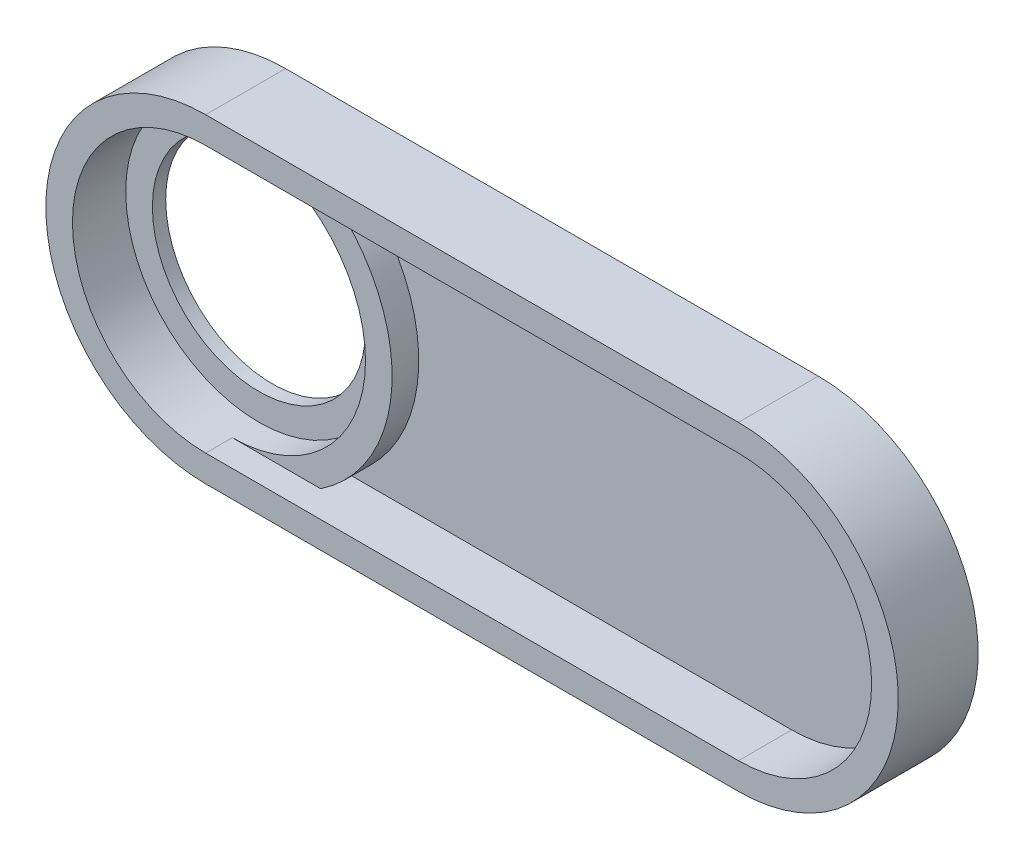
SolidWorks part; units mm, degrees
ref_plane "Front Plane" through (0, 0, 0) normal (0, 0, 1) x (1, 0, 0)
ref_plane "Top Plane" through (0, 0, 0) normal (0, 1, 0) x (1, 0, 0)
ref_plane "Right Plane" through (0, 0, 0) normal (1, 0, 0) x (0, 0, -1)
sketch "Sketch1" plane through (0, 0, 0) normal (0, 0, 1) x (1, 0, 0)
  line L0 (0, 0) -> (200, 0) construction
  line L1 (0, 60) -> (200, 60)
  line L2 (0, -60) -> (200, -60)
  arc A0 (0, 60) -> (0, -60) centre (0, 0) ccw
  arc A1 (200, -60) -> (200, 60) centre (200, 0) ccw
  circle A2 centre (0, 0) radius 40
  point P2 (100, 0)
  dimension "D3" = 80
  dimension "D1" = 60
  dimension "D2" = 200
extrude "Boss-Extrude1" add sketch "Sketch1" along normal blind 10
sketch "Sketch2" plane through (0, 0, 0) normal (0, 0, -1) x (-1, 0, 0)
  circle A0 centre (0, 0) radius 52.5
  dimension "D1" = 105
extrude "Cut-Extrude1" cut sketch "Sketch2" against normal blind 5
sketch "Sketch3" plane through (0, 0, 10) normal (0, 0, 1) x (1, 0, 0)
  circle A0 centre (0, 0) radius 40 construction
  circle A1 centre (0, 0) radius 40
  circle A2 centre (0, 0) radius 50
  circle A3 centre (0, 0) radius 60
  arc A4 (0, 60) -> (0, -60) centre (0, 0) ccw construction
  arc M1 (0, 60) -> (0, -60) centre (0, 0) ccw
  dimension "D1" = 100
extrude "Boss-Extrude2" add sketch "Sketch3" along normal blind 10 contours A3 A2 M1
sketch "Sketch4" plane through (0, 0, 10) normal (0, 0, 1) x (1, 0, 0)
  line L0 (0, -60) -> (200, -60) construction
  line L1 (200, 60) -> (0, 60) construction
  line L2 (0, -60) -> (200, -60)
  line L3 (200, 60) -> (0, 60)
  line L4 (0, -50) -> (200, -50)
  line L5 (200, 50) -> (0, 50)
  circle A1 centre (0, 0) radius 60 construction
  arc A2 (200, -60) -> (200, 60) centre (200, 0) ccw construction
  arc A4 (0, 60) -> (0, -60) centre (0, 0) ccw
  arc A5 (200, -60) -> (200, 60) centre (200, 0) ccw
  arc A6 (200, -50) -> (200, 50) centre (200, 0) ccw
  arc A7 (0, 50) -> (0, -50) centre (0, 0) ccw
  dimension "D1" = 10
extrude "Boss-Extrude3" add sketch "Sketch4" along normal blind 20
